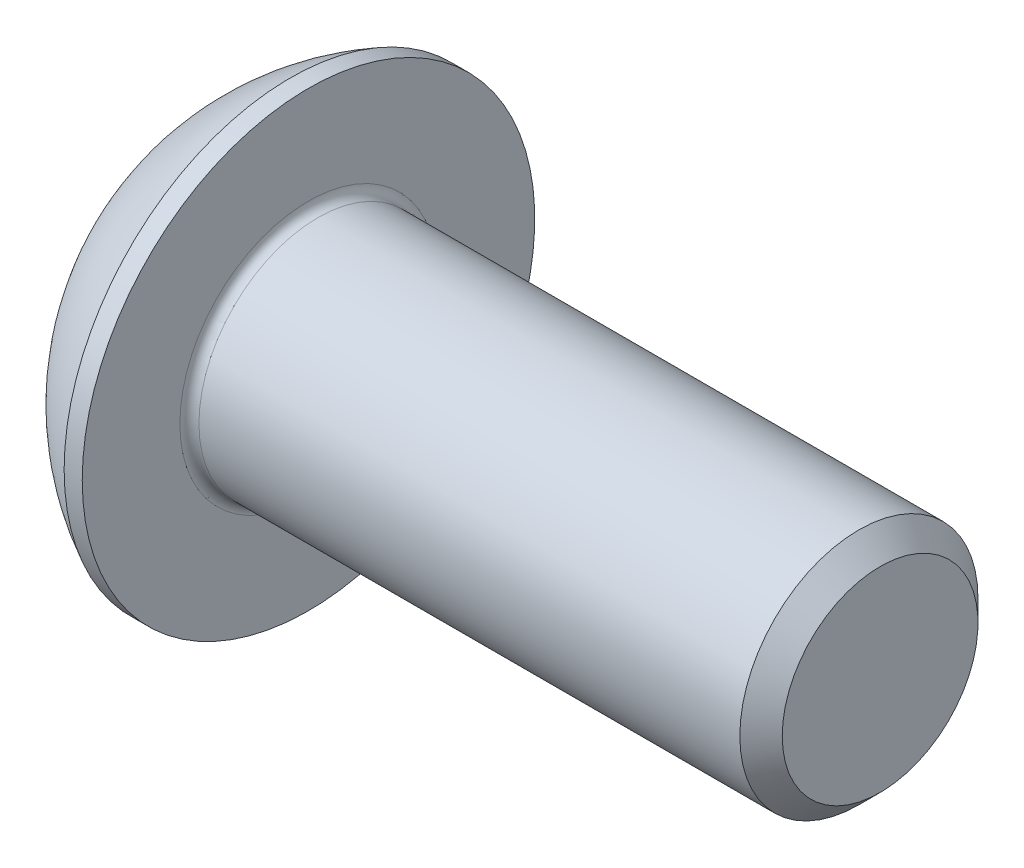
SolidWorks part; units mm, degrees
ref_plane "Plane1" through (0, 0, 0) normal (0, 0, 1) x (1, 0, 0)
ref_plane "Plane2" through (0, 0, 0) normal (0, 1, 0) x (1, 0, 0)
ref_plane "Plane3" through (0, 0, 0) normal (1, 0, 0) x (0, 0, -1)
sketch "BodySke" plane through (0, 0, 0) normal (0, 0, 1) x (1, 0, 0)
  line L0 (14.75, 0) -> (14.75, 2.055)
  line L1 (14.305, 2.5) -> (2.75, 2.5)
  line L2 (2.75, 2.5) -> (2.75, 4.75)
  line L3 (2.75, 4.75) -> (2.37, 4.75)
  line L4 (0, 0) -> (101.6, 0) construction
  line L5 (2.75, -4.75) -> (2.37, -4.75) construction
  line L6 (55.6768, -2.5) -> (2.75, -2.5) construction
  line L7 (14.75, 0) -> (0, 0)
  line L8 (0, 2.375) -> (0, -2.375) construction
  line L9 (0, 0) -> (0, 2.375)
  line L10 (14.75, 2.055) -> (14.305, 2.5)
  line L11 (14.75, -2.055) -> (14.305, -2.5) construction
  line L12 (3.55, 9.525) -> (3.55, -2.5) construction
  line L13 (2.75, 9.525) -> (2.75, -2.5) construction
  arc A1 (0, 2.375) -> (2.37, 4.75) centre (4.755, 0) cw
  dimension "D1" = 4.75
  dimension "Diameter" = 5
  dimension "Length" = 12
  dimension "Head_dia" = 9.5
  dimension "Head_ht" = 2.75
  dimension "Head_side_ht" = 0.38
  dimension "Minor_dia" = 4.11
  dimension "Body_ch_ang" = 45
  dimension "Advance" = 0.8
  dimension "Thread_nom" = 12
revolve "BaseBody" add sketch "BodySke" angle 360 about L4
cosmetic thread "ThreadCosmetic"
fillet "Fillet1" radius 0.2 1 edges at (2.75, 0, 2.5)
sketch "Sketch2" plane through (0, 0, 0) normal (0, 0, 1) x (1, 0, 0)
  line L0 (0, 1.5) -> (1.56, 1.5)
  line L1 (1.56, 1.5) -> (2.426, 0)
  line L3 (2.426, 0) -> (0, 0)
  line L4 (0, 0) -> (0, 1.5)
  line L5 (0, -1.5) -> (1.56, -1.5) construction
  line L6 (0, 0) -> (47.625, 0) construction
  dimension "D2" = 60
  dimension "PreBroach_depth" = 1.56
  dimension "PreBroach_dia" = 3
revolve "PreBroach" cut sketch "Sketch2" angle 360 about L6
sketch "Sketch3" plane through (0, 0, 0) normal (1, 0, 0) x (0, 0, -1)
  line L0 (-1.5, -0.866) -> (-1.5, 0.866)
  line L1 (-1.5, 0.866) -> (0, 1.7321)
  line L2 (0, 1.7321) -> (1.5, 0.866)
  line L3 (1.5, 0.866) -> (1.5, -0.866)
  line L4 (1.5, -0.866) -> (0, -1.7321)
  line L5 (0, -1.7321) -> (-1.5, -0.866)
  dimension "D1" = 1.5
  dimension "D2" = 1.5
  dimension "D3" = 3
  dimension "Hex_size" = 3
extrude "Hex" cut sketch "Sketch3" along normal blind 1.56
sketch "ThdSchSke" plane through (0, 0, 0) normal (0, 0, 1) x (1, 0, 0)
  line L0 (4.35, -2.055) -> (4.0384, -2.5)
  line L1 (4.35, -2.055) -> (4.6616, -2.5)
  line L2 (4.6616, -2.5) -> (4.6616, -3.125)
  line L3 (-3.175, 0) -> (5.1513, 0) construction
  line L5 (4.6616, -3.125) -> (4.0384, -3.125)
  line L6 (4.0384, -3.125) -> (4.0384, -2.5)
  dimension "Thread_minor" = 4.11
  dimension "Diameter" = 5
  dimension "Start" = 4.35
  dimension "SideAngle" = 55
  dimension "VeeAngle" = 70
  dimension "Overcut" = 6.25
revolve "ThreadSchematic" [suppressed] cut sketch "ThdSchSke" angle 360 about L3
pattern_linear "ThdSchPat" [suppressed]
equation "\"D1@BodySke\" = \"Head_dia@BodySke\" * .5"
equation "\"Thread_minor@ThreadCosmetic\" = \"Minor_dia@BodySke\""
equation "\"D1@Sketch3\" = \"Hex_size@Sketch3\" / 2"
equation "\"D2@Sketch3\" = \"D1@Sketch3\""
equation "\"D3@Sketch3\" = \"Hex_size@Sketch3\""
equation "\"Thread_length@ThreadCosmetic\" = ((sgn( (\"Length@BodySke\" - \"Advance@BodySke\" * 2.0) - \"Thread_nom@BodySke\" )-1)*( (\"Length@BodySke\" - \"Advance@BodySke\" * 2.0) - \"Thread_nom@BodySke\" ))/-2+ \"Thread_nom@BodySke\""
equation "\"Thread_minor@ThdSchSke\" = \"Minor_dia@BodySke\""
equation "\"Diameter@ThdSchSke\" = \"Diameter@BodySke\""
equation "\"Overcut@ThdSchSke\" = \"Diameter@BodySke\" * 1.25"
equation "\"Start@ThdSchSke\" = \"Head_ht@BodySke\" + \"Length@BodySke\" - \"Thread_length@ThreadCosmetic\"  '---Non-countersunk---"
equation "\"Num_threads@ThdSchPat\" = int( \"Thread_length@ThreadCosmetic\" / \"Advance@BodySke\" + 0.999 )  + 1"
equation "\"Advance@ThdSchPat\" = \"Thread_length@ThreadCosmetic\" /  (\"Num_threads@ThdSchPat\" - 1) 'relax it"
equation "\"Num_threads@ThdSchPat\" = \"Num_threads@ThdSchPat\" - sgn( \"Num_threads@ThdSchPat\" - 1) '---chamfered tips only---"
